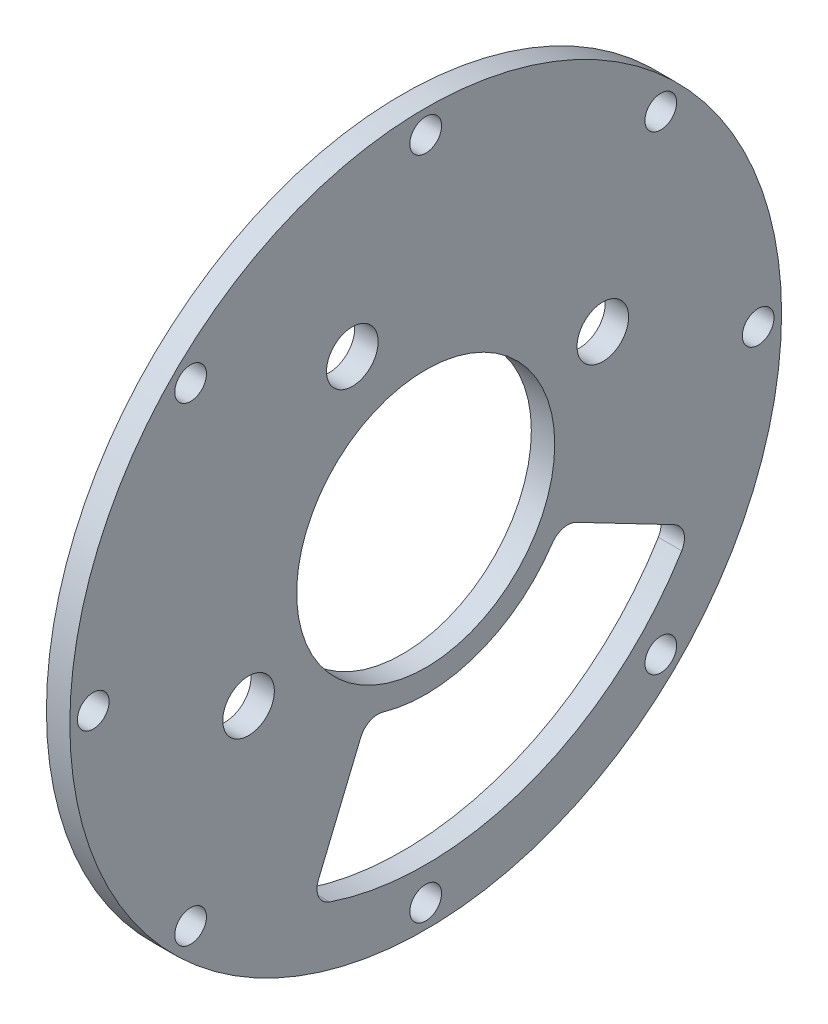
SolidWorks part; units mm, degrees
ref_plane "Front Plane" through (0, 0, 0) normal (0, 0, 1) x (1, 0, 0)
ref_plane "Top Plane" through (0, 0, 0) normal (0, 1, 0) x (1, 0, 0)
ref_plane "Right Plane" through (0, 0, 0) normal (1, 0, 0) x (0, 0, -1)
sketch "Sketch5" plane through (0, 0, 0) normal (1, 0, 0) x (0, 0, -1)
  line L0 (9.9498, 24.0209) -> (0, 0) construction
  line L1 (20.4349, -10.6377) -> (33.7199, -17.5535)
  line L2 (24.0182, 9.948) -> (-24.0238, -9.9508) construction
  line L3 (0, 0) -> (-4.1204, 9.948) construction
  line L4 (0, 0) -> (-13.6375, 5.6491) construction
  line L6 (-8.8162, -21.2842) -> (-14.5478, -35.1215)
  circle A0 centre (0, 0) radius 17.5 construction
  circle A1 centre (0, 0) radius 48.26
  circle A2 centre (0, 45.085) radius 2.1527
  circle A3 centre (-24.0238, -9.9508) radius 3.5
  circle A4 centre (31.8799, 31.8799) radius 2.1527
  circle A5 centre (45.085, 0) radius 2.1527
  circle A6 centre (24.0182, 9.948) radius 3.5
  circle A7 centre (-9.9504, 24.024) radius 3.5
  circle A13 centre (31.8799, -31.8799) radius 2.1526
  circle A14 centre (0, -45.085) radius 2.1527
  circle A15 centre (-31.8799, -31.8799) radius 2.1526
  circle A16 centre (-45.085, 0) radius 2.1526
  circle A17 centre (-31.8799, 31.8799) radius 2.1526
  circle A19 centre (0, 0) radius 17.5
  arc A27 (20.4349, -10.6377) -> (17.1511, -11.478) centre (19.262, -12.8907) ccw
  arc A31 (33.7199, -17.5535) -> (34.7169, -21.1269) centre (32.5471, -19.8065) cw
  arc A39 (34.7169, -21.1269) -> (-13.0146, -38.4998) centre (0, 0) cw
  arc A40 (-13.0146, -38.4998) -> (-14.5478, -35.1215) centre (-12.2011, -36.0935) cw
  arc A41 (-5.7606, -19.8172) -> (-8.8162, -21.2842) centre (-6.4696, -22.2563) ccw
  arc A42 (17.1511, -11.478) -> (-5.7606, -19.8172) centre (0, 0) cw
  dimension "D4" = 45.085
  dimension "D5" = 45
  dimension "D6" = 35
  dimension "D8" = 7
  dimension "D9" = 52
  dimension "D2" = 96.52
  dimension "D3" = 4.3053
  dimension "D7" = 7
  dimension "D11" = 26
extrude "Boss-Extrude3" add sketch "Sketch5" along normal blind 3.175
